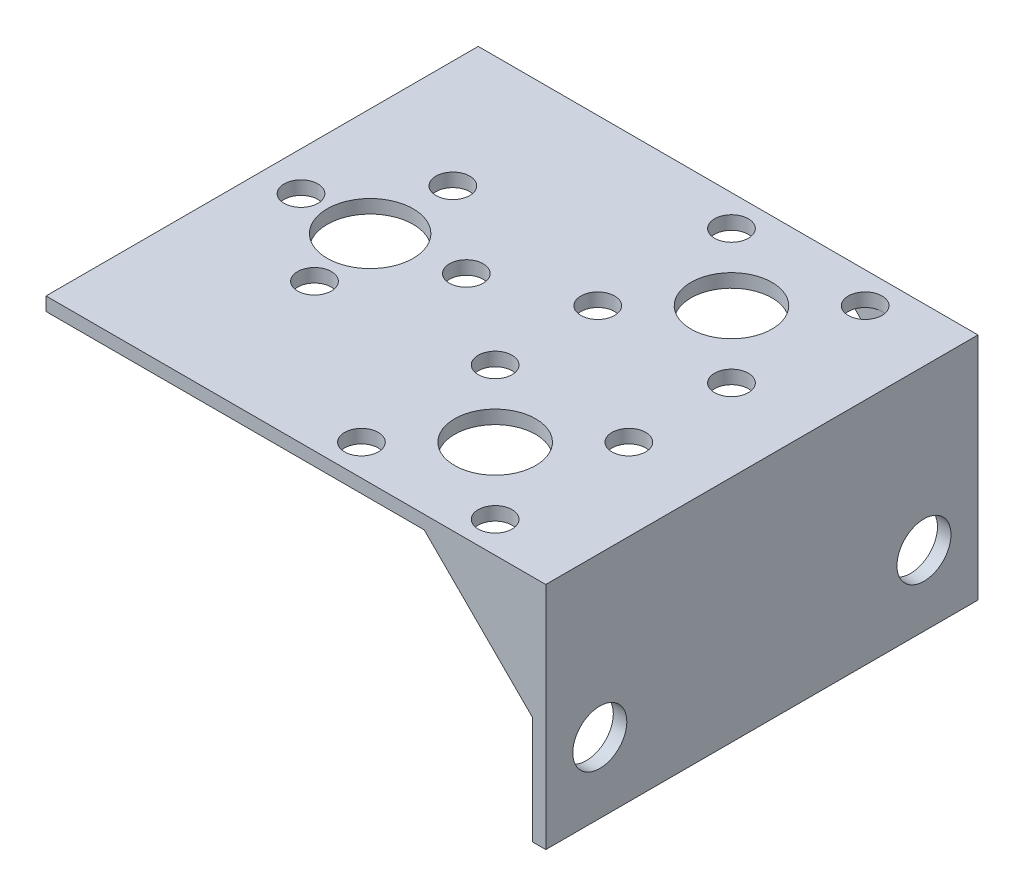
SolidWorks part; units mm, degrees
material "AISI 1020"
ref_plane "Front Plane" through (0, 0, 0) normal (0, 0, 1) x (1, 0, 0)
ref_plane "Top Plane" through (0, 0, 0) normal (0, 1, 0) x (1, 0, 0)
ref_plane "Right Plane" through (0, 0, 0) normal (1, 0, 0) x (0, 0, -1)
sketch "Sketch3" plane through (0, 0, 0) normal (0, 0, 1) x (1, 0, 0)
  line L0 (-121.2197, 0) -> (-62.4822, 0)
  line L1 (-62.4822, 0) -> (-62.4822, -26.9875)
  line L5 (-64.0697, -26.9875) -> (-64.0697, -1.5875)
  line L6 (-64.0697, -1.5875) -> (-121.2197, -1.5875)
  line L7 (-121.2197, -1.5875) -> (-121.2197, 0)
  line L9 (-62.4822, -26.9875) -> (-64.0697, -26.9875)
  point P3 (-63.2759, -26.9875)
  dimension "D1" = 25.4
  dimension "D2" = 1.5875
  dimension "D3" = 1.5875
  dimension "D4" = 57.15
extrude "Boss-Extrude2" add sketch "Sketch3" along normal blind 50.8
sketch "Sketch4" plane through (0, 0, 0) normal (0, 1, 0) x (1, 0, 0)
  line L0 (-121.2197, -50.8) -> (-121.2197, 0) construction
  line L1 (-68.8322, -50.4) -> (-91.0572, -50.4) construction
  line L2 (-68.8322, -50.4) -> (-68.8322, -28.175) construction
  line L3 (-68.8322, -28.175) -> (-91.0572, -28.175) construction
  line L4 (-121.2197, -25.4) -> (-62.5425, -25.4) construction
  line L6 (-79.9447, -39.2875) -> (-79.9447, -11.5125) construction
  line L7 (-91.0572, -50.4) -> (-91.0572, -28.175) construction
  line L8 (-68.8322, -50.4) -> (-91.0572, -28.175) construction
  line L9 (-68.8322, -28.175) -> (-91.0572, -50.4) construction
  line L10 (-68.8322, -22.625) -> (-91.0572, -0.4) construction
  line L12 (-68.8322, -0.4) -> (-91.0572, -22.625) construction
  line L13 (-91.0572, -0.4) -> (-91.0572, -22.625) construction
  line L14 (-68.8322, -22.625) -> (-91.0572, -22.625) construction
  line L15 (-68.8322, -0.4) -> (-68.8322, -22.625) construction
  line L16 (-68.8322, -0.4) -> (-91.0572, -0.4) construction
  circle A0 centre (-108.5197, -25.4) radius 5.05
  circle A5 centre (-79.9447, -39.2875) radius 4.7625
  circle A6 centre (-79.9447, -39.2875) radius 11.1125 construction
  circle A17 centre (-108.5197, -15.685) radius 1.9844
  circle A18 centre (-87.8024, -31.4298) radius 1.9844
  circle A19 centre (-72.0869, -31.4298) radius 1.9844
  circle A20 centre (-72.0869, -47.1452) radius 1.9844
  circle A21 centre (-87.8024, -47.1452) radius 1.9844
  circle A22 centre (-116.6497, -25.4) radius 1.9844
  circle A26 centre (-98.8047, -23.815) radius 1.9844
  circle A27 centre (-106.9347, -33.53) radius 1.9844
  circle A29 centre (-79.9447, -11.5125) radius 11.1125 construction
  circle A30 centre (-87.8024, -3.6548) radius 1.9844
  circle A31 centre (-72.0869, -3.6548) radius 1.9844
  circle A32 centre (-72.0869, -19.3702) radius 1.9844
  circle A33 centre (-87.8024, -19.3702) radius 1.9844
  circle A34 centre (-79.9447, -11.5125) radius 4.7625
  point P13 (-91.8811, -25.4)
  point P22 (0, 0)
  point P29 (0, 0)
  point P30 (-62.4822, -23.815)
  point P34 (0, 0)
  point P35 (-63.495, -23.815)
  point P50 (-62.5425, -25.4)
  point P51 (-79.9447, -38.8875)
  dimension "D1" = 10.1
  dimension "D2" = 27.775
  dimension "D3" = 22.225
  dimension "D4" = 11.1125
  dimension "D5" = 9.525
  dimension "D7" = 4
  dimension "D6" = 3.9688
  dimension "D8" = 3.9688
  dimension "D9" = 8.13
  dimension "D11" = 12.7
  dimension "D10" = 28.575
extrude "Cut-Extrude1" cut sketch "Sketch4" against normal up to surface (1.5875 mm away) up to face at (-92.6447, -1.5875, 25.4)
sketch "Sketch5" plane through (0, 0, 0) normal (0, 0, -1) x (-1, 0, 0)
  line L0 (76.7697, -1.5875) -> (64.0697, -14.2875)
  line L1 (121.2197, -1.5875) -> (64.0697, -1.5875) construction
  line L2 (64.0697, -1.5875) -> (64.0697, -26.9875) construction
  line L3 (64.0697, -14.2875) -> (64.0697, -1.5875)
  line L4 (64.0697, -1.5875) -> (76.7697, -1.5875)
  dimension "D1" = 12.7
  dimension "D2" = 12.7
extrude "Boss-Extrude3" add sketch "Sketch5" against normal blind 1.5875
sketch "Sketch7" plane through (0, 0, 50.8) normal (0, 0, 1) x (1, 0, 0)
  line L0 (-64.0697, -1.5875) -> (-64.0697, -14.2875)
  line L1 (-64.0697, -1.5875) -> (-64.0697, -26.9875) construction
  line L2 (-64.0697, -14.2875) -> (-76.7697, -1.5875)
  line L3 (-121.2197, -1.5875) -> (-64.0697, -1.5875) construction
  line L4 (-76.7697, -1.5875) -> (-64.0697, -1.5875)
  dimension "D1" = 12.7
  dimension "D2" = 12.7
extrude "Boss-Extrude4" add sketch "Sketch7" against normal blind 1.5875
sketch "Sketch8" plane through (-62.4822, 0, 0) normal (1, 0, 0) x (0, 0, -1)
  line L0 (-44.45, -18.7254) -> (-6.35, -18.7254) construction
  line L1 (-50.8, -26.9875) -> (-50.8, 0) construction
  circle A0 centre (-44.45, -18.7254) radius 3.175
  circle A1 centre (-6.35, -18.7254) radius 3.175
  dimension "D1" = 6.35
  dimension "D2" = 6.35
  dimension "D3" = 38.1
  dimension "D4" = 6.35
extrude "Cut-Extrude2" cut sketch "Sketch8" against normal up to surface (1.5875 mm away) up to face at (-64.0697, -14.2875, 25.4)
